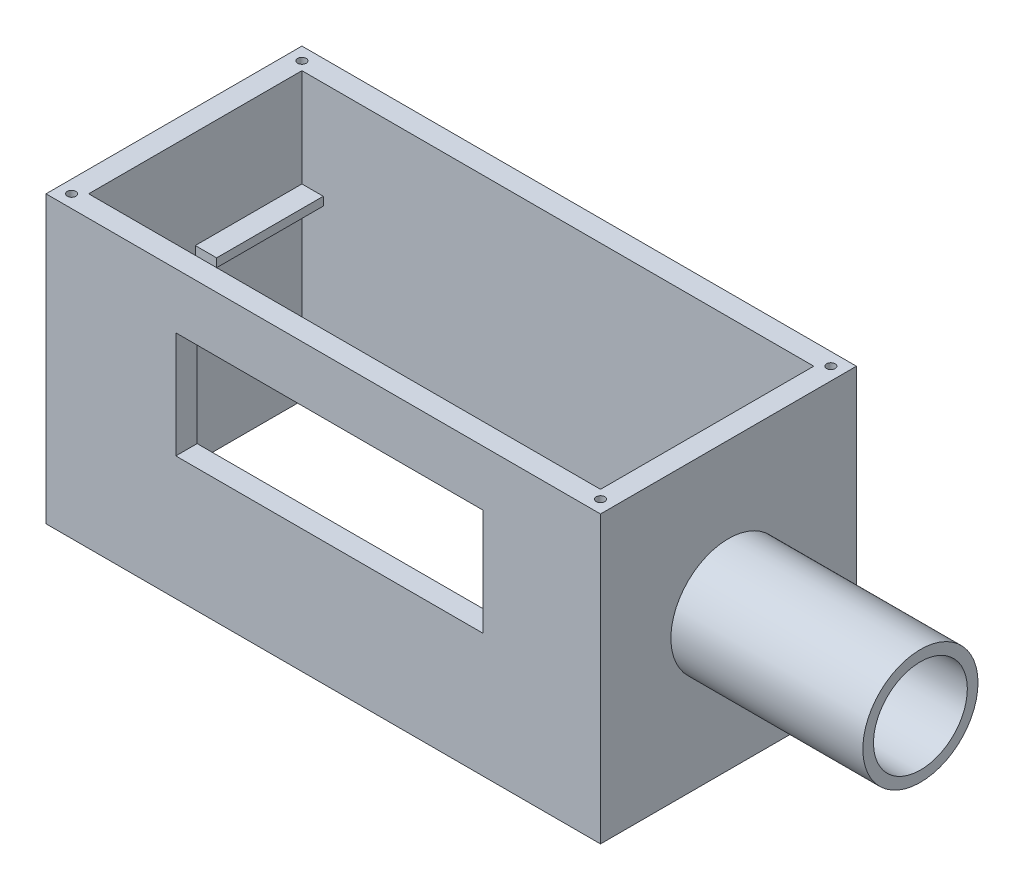
SolidWorks part; units mm, degrees
ref_plane "Front Plane" through (0, 0, 0) normal (0, 0, 1) x (1, 0, 0)
ref_plane "Top Plane" through (0, 0, 0) normal (0, 1, 0) x (1, 0, 0)
ref_plane "Right Plane" through (0, 0, 0) normal (1, 0, 0) x (0, 0, -1)
sketch "Sketch1" plane through (0, 0, 0) normal (0, 1, 0) x (1, 0, 0)
  line L1 (-65, 30) -> (65, 30)
  line L2 (-65, 30) -> (-65, -30)
  line L3 (-65, -30) -> (65, -30)
  line L4 (65, 30) -> (65, -30)
  line L5 (-65, 30) -> (65, -30) construction
  line L6 (-65, -30) -> (65, 30) construction
  point P0 (0, 0)
  dimension "D1" = 60
  dimension "D2" = 130
extrude "Boss-Extrude1" add sketch "Sketch1" along normal blind 67
sketch "Sketch2" plane through (0, 67, 0) normal (0, 1, 0) x (1, 0, 0)
  line L0 (-65, -30) -> (65, -30) construction
  line L1 (-60, 25) -> (60, 25)
  line L2 (-60, 25) -> (-60, -25)
  line L3 (-60, -25) -> (60, -25)
  line L4 (60, 25) -> (60, -25)
  line L5 (-60, 25) -> (60, -25) construction
  line L6 (-60, -25) -> (60, 25) construction
  line L7 (-65, 30) -> (-65, -30) construction
  point P0 (0, 0)
  dimension "D1" = 5
  dimension "D2" = 5
extrude "Cut-Extrude1" cut sketch "Sketch2" against normal up to next
sketch "Sketch4" plane through (60, 0, 0) normal (-1, 0, 0) x (0, 0, 1)
  line L0 (30, 0) -> (-30, 0) construction
  line L1 (0.2384, 44) -> (-27.5, 44)
  line L2 (0.2384, 44) -> (0.2384, 42)
  line L3 (0.2384, 42) -> (-27.5, 42)
  line L4 (-27.5, 44) -> (-27.5, 42)
  line L5 (0.2384, 44) -> (-27.5, 42) construction
  line L6 (0.2384, 42) -> (-27.5, 44) construction
  line L7 (-30, 67) -> (-30, 0) construction
  point P0 (-13.6308, 43)
  dimension "D1" = 42
  dimension "D2" = 2
  dimension "D3" = 2.5
extrude "Boss-Extrude2" add sketch "Sketch4" along normal blind 5
sketch "Sketch5" plane through (-60, 0, 0) normal (1, 0, 0) x (0, 0, -1)
  line L0 (-30, 0) -> (30, 0) construction
  line L1 (0, 44) -> (27.5, 44)
  line L2 (0, 44) -> (0, 42)
  line L3 (0, 42) -> (27.5, 42)
  line L4 (27.5, 44) -> (27.5, 42)
  line L5 (30, 67) -> (30, 0) construction
  dimension "D1" = 42
  dimension "D2" = 2.5
  dimension "D3" = 2
extrude "Boss-Extrude3" add sketch "Sketch5" along normal blind 5
sketch "Sketch6" plane through (0, 0, 30) normal (0, 0, 1) x (1, 0, 0)
  line L0 (-65, 0) -> (65, 0) construction
  line L1 (-34.5641, 54) -> (37.4359, 54)
  line L2 (-34.5641, 54) -> (-34.5641, 29)
  line L3 (-34.5641, 29) -> (37.4359, 29)
  line L4 (37.4359, 54) -> (37.4359, 29)
  line L5 (-34.5641, 54) -> (37.4359, 29) construction
  line L6 (-34.5641, 29) -> (37.4359, 54) construction
  point P0 (1.4359, 41.5)
  dimension "D1" = 72
  dimension "D2" = 25
  dimension "D3" = 29
extrude "Cut-Extrude2" cut sketch "Sketch6" against normal up to next
sketch "Sketch8" plane through (0, 67, 0) normal (0, 1, 0) x (1, 0, 0)
  line L0 (65, 30) -> (-65, 30) construction
  line L1 (65, -30) -> (65, 30) construction
  line L3 (-65, 30) -> (-65, -30) construction
  line L4 (65, 30) -> (-65, 30) construction
  line L5 (-65, 30) -> (-65, -30) construction
  line L6 (-65, -30) -> (65, -30) construction
  circle A0 centre (-62, 27) radius 1
  circle A1 centre (62, 27) radius 1
  circle A2 centre (-62, -27) radius 1
  circle A3 centre (62, -27) radius 1
  point P13 (0, 0)
  point P15 (0, 0)
  dimension "D1" = 2
  dimension "D2" = 3
  dimension "D3" = 3
  dimension "D4" = 3
  dimension "D5" = 3
  dimension "D6" = 3
  dimension "D7" = 3
  dimension "D8" = 3
  dimension "D9" = 3
extrude "Cut-Extrude3" cut sketch "Sketch8" against normal up to next
sketch "Sketch9" plane through (65, 0, 0) normal (1, 0, 0) x (0, 0, -1)
  line L0 (-30, 0) -> (30, 0) construction
  circle A0 centre (0, 33.5) radius 13.5
  dimension "D1" = 27
  dimension "D2" = 33.5
extrude "Boss-Extrude4" add sketch "Sketch9" along normal blind 45
sketch "Sketch10" plane through (110, 0, 0) normal (1, 0, 0) x (0, 0, -1)
  line L0 (-30, 0) -> (30, 0) construction
  circle A0 centre (0, 33.5) radius 11
  dimension "D1" = 22
  dimension "D2" = 33.5
extrude "Cut-Extrude4" cut sketch "Sketch10" against normal blind 45
